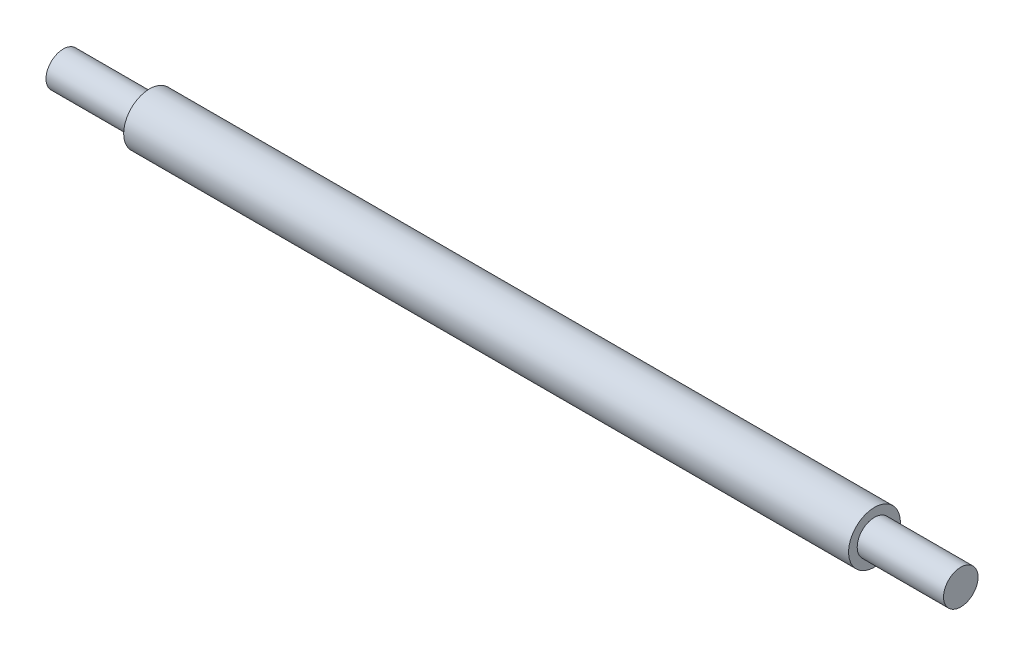
SolidWorks part; units mm, degrees
ref_plane "Front Plane" through (0, 0, 0) normal (0, 0, 1) x (1, 0, 0)
ref_plane "Top Plane" through (0, 0, 0) normal (0, 1, 0) x (1, 0, 0)
ref_plane "Right Plane" through (0, 0, 0) normal (1, 0, 0) x (0, 0, -1)
sketch "Sketch1" plane through (0, 0, 0) normal (0, 0, 1) x (1, 0, 0)
  line L0 (-52, 0) -> (52, 0)
  line L1 (-52, 0) -> (-52, 2)
  line L2 (-52, 2) -> (-42, 2)
  line L3 (-42, 2) -> (-42, 3)
  line L4 (-42, 3) -> (42, 3)
  line L6 (42, 2) -> (42, 3)
  line L7 (52, 0) -> (52, 2)
  line L8 (52, 2) -> (42, 2)
  point P4 (0, 0)
revolve "Revolve1" add sketch "Sketch1" angle 360 about L0
